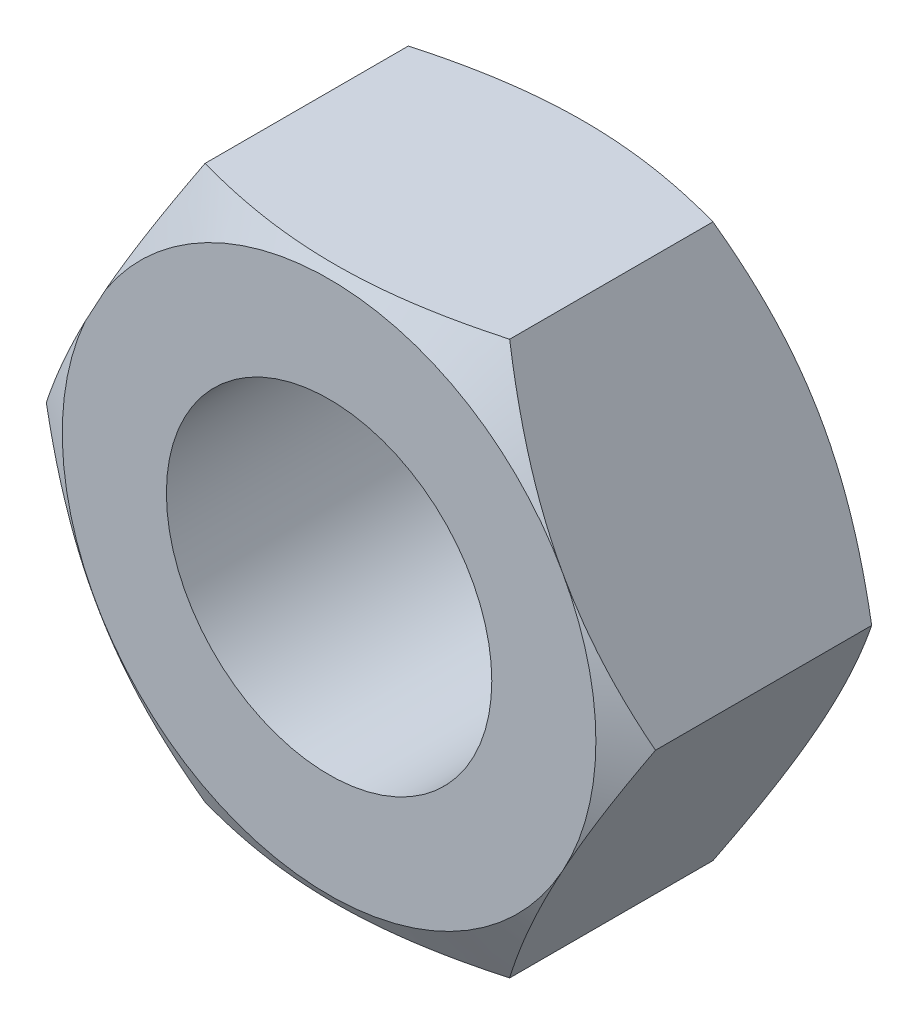
SolidWorks part; units mm, degrees
ref_plane "Front Plane" through (0, 0, 0) normal (0, 0, 1) x (1, 0, 0)
ref_plane "Top Plane" through (0, 0, 0) normal (0, 1, 0) x (1, 0, 0)
ref_plane "Right Plane" through (0, 0, 0) normal (1, 0, 0) x (0, 0, -1)
sketch "Sketch1" plane through (0, 0, 0) normal (0, 0, 1) x (1, 0, 0)
  line L0 (-14.6891, 0) -> (16.0354, 0) construction
  line L1 (9.3597, 0) -> (4.68, 8.5)
  line L2 (4.68, 8.5) -> (-4.68, 8.5)
  line L3 (-4.68, 8.5) -> (-9.36, -0.106)
  line L4 (-9.36, -0.106) -> (-4.68, -8.5)
  line L5 (-4.68, -8.5) -> (4.68, -8.5)
  line L6 (4.68, -8.5) -> (9.3597, 0)
  dimension "D1" = 18.72
  dimension "D2" = 8.5
  dimension "D3" = 8.5
extrude "Boss-Extrude1" add sketch "Sketch1" along normal blind 8 contours L2 L3 L4 L5 L6 L1
sketch "Sketch2" plane through (0, 0, 8) normal (0, 0, 1) x (1, 0, 0)
  circle A0 centre (0, 0) radius 8.1992
extrude "Cut-Extrude1" cut sketch "Sketch2" against normal blind 10 draft 60 flip side to cut
sketch "Sketch3" plane through (0, 0, 0) normal (0, 0, -1) x (-1, 0, 0)
  circle A0 centre (0, 0) radius 8.1722
extrude "Cut-Extrude2" cut sketch "Sketch3" against normal blind 1 draft 60 flip side to cut
sketch "Sketch4" plane through (0, 0, 8) normal (0, 0, 1) x (1, 0, 0)
  circle A0 centre (0, 0) radius 5
  dimension "D1" = 10
extrude "Cut-Extrude3" cut sketch "Sketch4" against normal blind 8
